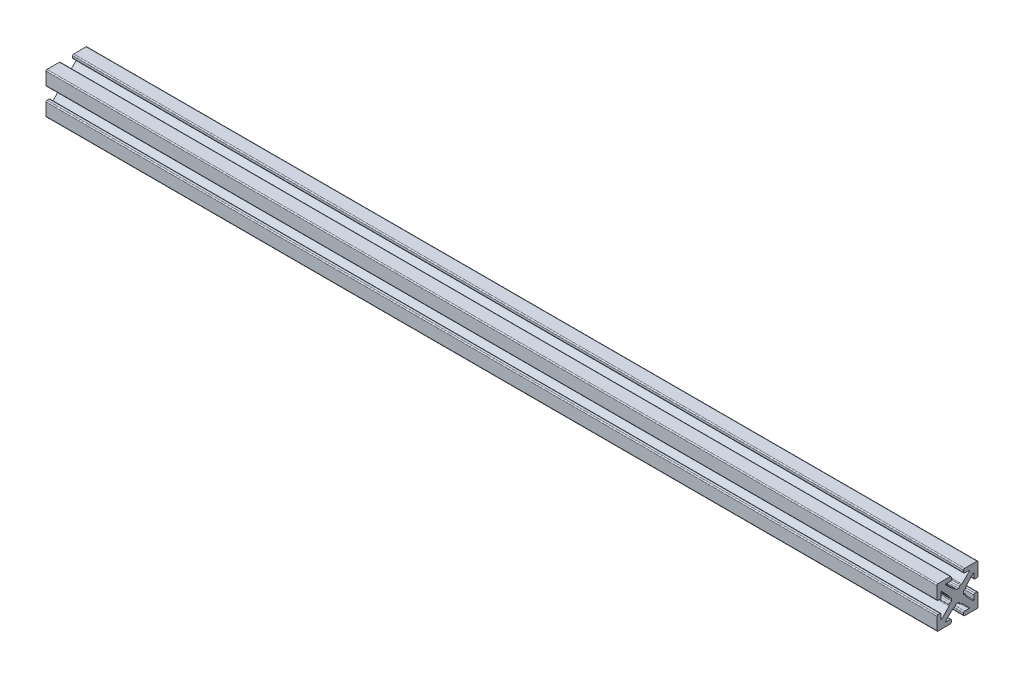
SolidWorks part; units mm, degrees
ref_plane "Front Plane" through (0, 0, 0) normal (0, 0, 1) x (1, 0, 0)
ref_plane "Top Plane" through (0, 0, 0) normal (0, 1, 0) x (1, 0, 0)
ref_plane "Right Plane" through (0, 0, 0) normal (1, 0, 0) x (0, 0, -1)
sketch "Sketch1" plane through (0, 0, 0) normal (1, 0, 0) x (0, 0, -1)
  line L0 (0, 0) -> (0, 1.4986) construction
  line L1 (-0.2413, 1.4986) -> (0.2413, 1.4986)
  line L2 (5.0038, 1.7526) -> (5.0038, 4.7498)
  line L3 (0.7493, 2.0066) -> (0.8899, 2.0066)
  line L4 (1.0639, 2.0756) -> (2.8908, 3.7937)
  line L5 (2.8038, 4.0132) -> (1.7526, 4.0132)
  line L6 (1.4986, 4.2672) -> (1.4986, 4.7498)
  line L7 (1.7526, 5.0038) -> (4.7498, 5.0038)
  line L8 (5.0038, 5.0038) -> (0, 0) construction
  line L9 (0, 0) -> (8.6271, 0) construction
  line L10 (0, 0) -> (0, 5.0038) construction
  line L11 (4.2672, 1.4986) -> (4.7498, 1.4986)
  line L12 (4.0132, 2.8038) -> (4.0132, 1.7526)
  line L13 (2.0756, 1.0639) -> (3.7937, 2.8908)
  line L14 (2.0066, 0.7493) -> (2.0066, 0.8899)
  line L15 (1.4986, -0.2413) -> (1.4986, 0.2413)
  line L16 (0, 0) -> (1.4986, 0) construction
  line L17 (-0.2413, -1.4986) -> (0.2413, -1.4986)
  line L18 (0.7493, -2.0066) -> (0.8899, -2.0066)
  line L19 (1.0639, -2.0756) -> (2.8908, -3.7937)
  line L20 (2.8038, -4.0132) -> (1.7526, -4.0132)
  line L21 (1.4986, -4.2672) -> (1.4986, -4.7498)
  line L22 (1.7526, -5.0038) -> (4.7498, -5.0038)
  line L23 (5.0038, -1.7526) -> (5.0038, -4.7498)
  line L24 (4.2672, -1.4986) -> (4.7498, -1.4986)
  line L25 (4.0132, -2.8038) -> (4.0132, -1.7526)
  line L26 (2.0756, -1.0639) -> (3.7937, -2.8908)
  line L27 (2.0066, -0.7493) -> (2.0066, -0.8899)
  line L28 (-0.7493, 2.0066) -> (-0.8899, 2.0066)
  line L29 (-1.0639, 2.0756) -> (-2.8908, 3.7937)
  line L30 (-2.8038, 4.0132) -> (-1.7526, 4.0132)
  line L31 (-1.4986, 4.2672) -> (-1.4986, 4.7498)
  line L32 (-1.7526, 5.0038) -> (-4.7498, 5.0038)
  line L33 (-5.0038, 1.7526) -> (-5.0038, 4.7498)
  line L34 (-4.2672, 1.4986) -> (-4.7498, 1.4986)
  line L35 (-4.0132, 2.8038) -> (-4.0132, 1.7526)
  line L36 (-2.0756, 1.0639) -> (-3.7937, 2.8908)
  line L37 (-2.0066, 0.7493) -> (-2.0066, 0.8899)
  line L38 (-1.4986, -0.2413) -> (-1.4986, 0.2413)
  line L39 (-2.0066, -0.7493) -> (-2.0066, -0.8899)
  line L40 (-2.0756, -1.0639) -> (-3.7937, -2.8908)
  line L41 (-4.0132, -2.8038) -> (-4.0132, -1.7526)
  line L42 (-4.2672, -1.4986) -> (-4.7498, -1.4986)
  line L43 (-5.0038, -1.7526) -> (-5.0038, -4.7498)
  line L44 (-1.7526, -5.0038) -> (-4.7498, -5.0038)
  line L45 (-1.4986, -4.2672) -> (-1.4986, -4.7498)
  line L46 (-2.8038, -4.0132) -> (-1.7526, -4.0132)
  line L47 (-1.0639, -2.0756) -> (-2.8908, -3.7937)
  line L48 (-0.7493, -2.0066) -> (-0.8899, -2.0066)
  arc A0 (2.8908, 3.7937) -> (2.8038, 4.0132) centre (2.8038, 3.8862) ccw
  arc A1 (0.4953, 1.7526) -> (0.7493, 2.0066) centre (0.7493, 1.7526) cw
  arc A2 (0.8899, 2.0066) -> (1.0639, 2.0756) centre (0.8899, 2.2606) ccw
  arc A3 (1.7526, 4.0132) -> (1.4986, 4.2672) centre (1.7526, 4.2672) cw
  arc A4 (1.4986, 4.7498) -> (1.7526, 5.0038) centre (1.7526, 4.7498) cw
  arc A5 (0.2413, 1.4986) -> (0.4953, 1.7526) centre (0.2413, 1.7526) ccw
  arc A6 (4.7498, 1.4986) -> (5.0038, 1.7526) centre (4.7498, 1.7526) ccw
  arc A7 (4.0132, 1.7526) -> (4.2672, 1.4986) centre (4.2672, 1.7526) ccw
  arc A8 (3.7937, 2.8908) -> (4.0132, 2.8038) centre (3.8862, 2.8038) cw
  arc A9 (2.0066, 0.8899) -> (2.0756, 1.0639) centre (2.2606, 0.8899) cw
  arc A10 (1.7526, 0.4953) -> (2.0066, 0.7493) centre (1.7526, 0.7493) ccw
  arc A11 (1.4986, 0.2413) -> (1.7526, 0.4953) centre (1.7526, 0.2413) cw
  arc A12 (0.2413, -1.4986) -> (0.4953, -1.7526) centre (0.2413, -1.7526) cw
  arc A13 (0.4953, -1.7526) -> (0.7493, -2.0066) centre (0.7493, -1.7526) ccw
  arc A14 (0.8899, -2.0066) -> (1.0639, -2.0756) centre (0.8899, -2.2606) cw
  arc A15 (2.8908, -3.7937) -> (2.8038, -4.0132) centre (2.8038, -3.8862) cw
  arc A16 (1.7526, -4.0132) -> (1.4986, -4.2672) centre (1.7526, -4.2672) ccw
  arc A17 (1.4986, -4.7498) -> (1.7526, -5.0038) centre (1.7526, -4.7498) ccw
  arc A18 (4.7498, -1.4986) -> (5.0038, -1.7526) centre (4.7498, -1.7526) cw
  arc A19 (4.0132, -1.7526) -> (4.2672, -1.4986) centre (4.2672, -1.7526) cw
  arc A20 (3.7937, -2.8908) -> (4.0132, -2.8038) centre (3.8862, -2.8038) ccw
  arc A21 (2.0066, -0.8899) -> (2.0756, -1.0639) centre (2.2606, -0.8899) ccw
  arc A22 (1.7526, -0.4953) -> (2.0066, -0.7493) centre (1.7526, -0.7493) cw
  arc A23 (1.4986, -0.2413) -> (1.7526, -0.4953) centre (1.7526, -0.2413) ccw
  arc A24 (-0.2413, 1.4986) -> (-0.4953, 1.7526) centre (-0.2413, 1.7526) cw
  arc A25 (-0.4953, 1.7526) -> (-0.7493, 2.0066) centre (-0.7493, 1.7526) ccw
  arc A26 (-0.8899, 2.0066) -> (-1.0639, 2.0756) centre (-0.8899, 2.2606) cw
  arc A27 (-2.8908, 3.7937) -> (-2.8038, 4.0132) centre (-2.8038, 3.8862) cw
  arc A28 (-1.7526, 4.0132) -> (-1.4986, 4.2672) centre (-1.7526, 4.2672) ccw
  arc A29 (-1.4986, 4.7498) -> (-1.7526, 5.0038) centre (-1.7526, 4.7498) ccw
  arc A30 (-4.7498, 1.4986) -> (-5.0038, 1.7526) centre (-4.7498, 1.7526) cw
  arc A31 (-4.0132, 1.7526) -> (-4.2672, 1.4986) centre (-4.2672, 1.7526) cw
  arc A32 (-3.7937, 2.8908) -> (-4.0132, 2.8038) centre (-3.8862, 2.8038) ccw
  arc A33 (-2.0066, 0.8899) -> (-2.0756, 1.0639) centre (-2.2606, 0.8899) ccw
  arc A34 (-1.7526, 0.4953) -> (-2.0066, 0.7493) centre (-1.7526, 0.7493) cw
  arc A35 (-1.4986, 0.2413) -> (-1.7526, 0.4953) centre (-1.7526, 0.2413) ccw
  arc A36 (-1.4986, -0.2413) -> (-1.7526, -0.4953) centre (-1.7526, -0.2413) cw
  arc A37 (-1.7526, -0.4953) -> (-2.0066, -0.7493) centre (-1.7526, -0.7493) ccw
  arc A38 (-2.0066, -0.8899) -> (-2.0756, -1.0639) centre (-2.2606, -0.8899) cw
  arc A39 (-3.7937, -2.8908) -> (-4.0132, -2.8038) centre (-3.8862, -2.8038) cw
  arc A40 (-4.0132, -1.7526) -> (-4.2672, -1.4986) centre (-4.2672, -1.7526) ccw
  arc A41 (-4.7498, -1.4986) -> (-5.0038, -1.7526) centre (-4.7498, -1.7526) ccw
  arc A42 (-1.4986, -4.7498) -> (-1.7526, -5.0038) centre (-1.7526, -4.7498) cw
  arc A43 (-1.7526, -4.0132) -> (-1.4986, -4.2672) centre (-1.7526, -4.2672) cw
  arc A44 (-2.8908, -3.7937) -> (-2.8038, -4.0132) centre (-2.8038, -3.8862) ccw
  arc A45 (-0.8899, -2.0066) -> (-1.0639, -2.0756) centre (-0.8899, -2.2606) ccw
  arc A46 (-0.4953, -1.7526) -> (-0.7493, -2.0066) centre (-0.7493, -1.7526) cw
  arc A47 (-0.2413, -1.4986) -> (-0.4953, -1.7526) centre (-0.2413, -1.7526) ccw
  arc A48 (-4.7498, 5.0038) -> (-5.0038, 4.7498) centre (-4.7498, 4.7498) ccw
  arc A49 (-5.0038, -4.7498) -> (-4.7498, -5.0038) centre (-4.7498, -4.7498) ccw
  arc A50 (4.7498, -5.0038) -> (5.0038, -4.7498) centre (4.7498, -4.7498) ccw
  arc A51 (4.7498, 5.0038) -> (5.0038, 4.7498) centre (4.7498, 4.7498) cw
  point P14 (3.1242, 4.0132)
  point P19 (0.9906, 2.0066)
  point P150 (0, -1.4986)
  point P152 (-5.0038, 5.0038)
  point P155 (-5.0038, -5.0038)
  point P158 (5.0038, -5.0038)
  dimension "D10" = 0.127
  dimension "D11" = 0.254
  dimension "D2" = 0.254
  dimension "D1" = 10.0076
  dimension "D3" = 2.9972
  dimension "D4" = 0.508
  dimension "D5" = 2.9972
  dimension "D6" = 0.9906
  dimension "D7" = 1.6256
  dimension "D8" = 1.9812
  dimension "D9" = 0.9906
extrude "Boss.-Extru.1" add sketch "Sketch1" along normal blind 217
